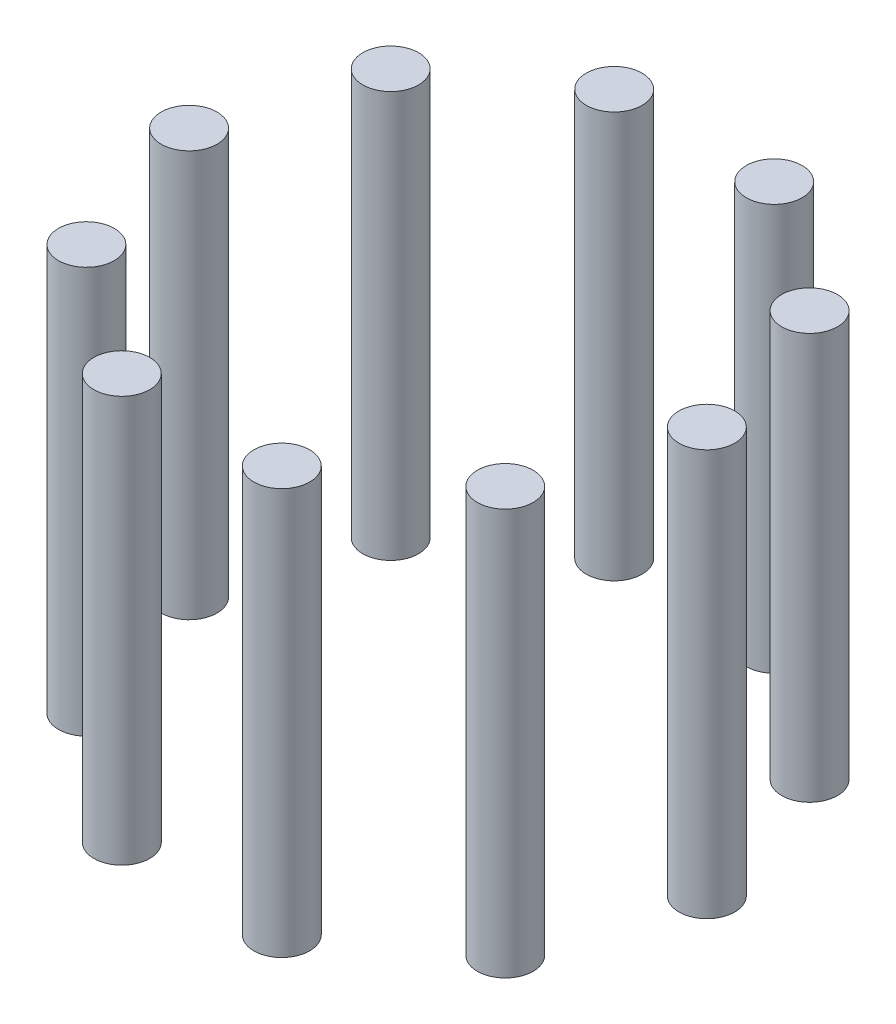
SolidWorks part; units mm, degrees
ref_plane "Front Plane" through (0, 0, 0) normal (0, 0, 1) x (1, 0, 0)
ref_plane "Top Plane" through (0, 0, 0) normal (0, 1, 0) x (1, 0, 0)
ref_plane "Right Plane" through (0, 0, 0) normal (1, 0, 0) x (0, 0, -1)
sketch "Sketch1" plane through (0, 0, 0) normal (0, 1, 0) x (1, 0, 0)
  circle A1 centre (51, 0) radius 5.5
  circle A2 centre (41.2599, -29.977) radius 5.5
  circle A3 centre (15.7599, -48.5039) radius 5.5
  circle A4 centre (-15.7599, -48.5039) radius 5.5
  circle A5 centre (-41.2599, -29.977) radius 5.5
  circle A6 centre (-51, 0) radius 5.5
  circle A7 centre (-41.2599, 29.977) radius 5.5
  circle A8 centre (-15.7599, 48.5039) radius 5.5
  circle A9 centre (15.7599, 48.5039) radius 5.5
  circle A10 centre (41.2599, 29.977) radius 5.5
  point P25 (0, 0)
  dimension "D1" = 10
extrude "Boss-Extrude1" add sketch "Sketch1" along normal blind 80
